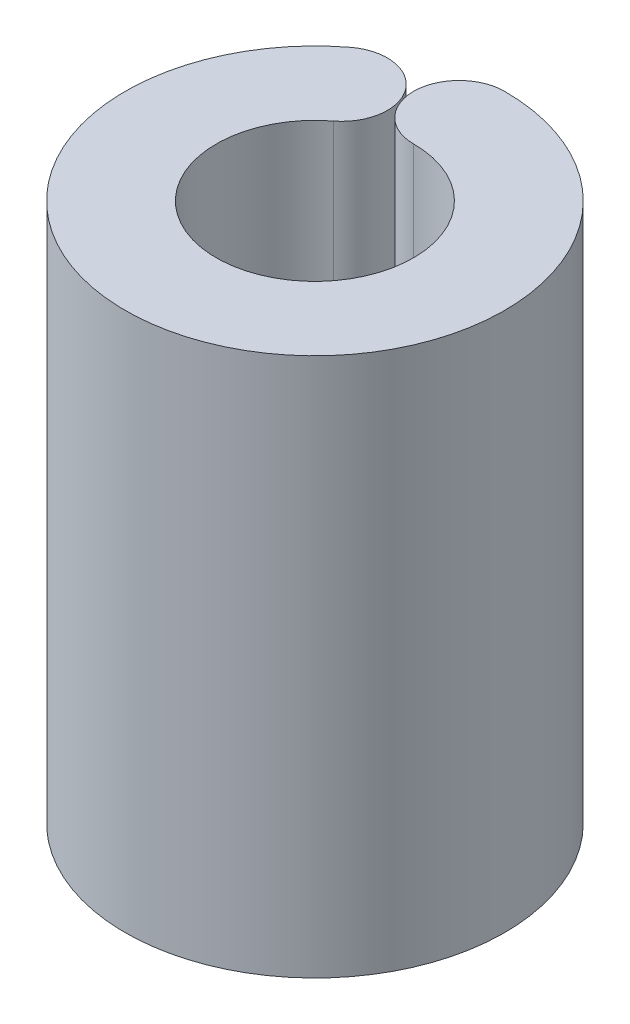
SolidWorks part; units mm, degrees
ref_plane "Front Plane" through (0, 0, 0) normal (0, 0, 1) x (1, 0, 0)
ref_plane "Top Plane" through (0, 0, 0) normal (0, 1, 0) x (1, 0, 0)
ref_plane "Right Plane" through (0, 0, 0) normal (1, 0, 0) x (0, 0, -1)
sketch "Sketch1" plane through (0, 0, 0) normal (0, 1, 0) x (1, 0, 0)
  arc A0 (0, 3.8) -> (-2.3089, 3.0181) centre (0, 0) cw
  arc A1 (0, 2.6) -> (-1.5798, 2.065) centre (0, 0) cw
  arc A2 (0, 5) -> (-3.038, 3.9712) centre (0, 0) cw
  arc A3 (0, 2.6) -> (0, 5) centre (0, 3.8) cw
  arc A4 (-1.5798, 2.065) -> (-3.038, 3.9712) centre (-2.3089, 3.0181) ccw
  dimension "D1" = 3.8
  dimension "D2" = 1.2
  dimension "D3" = 1.2
extrude "Boss-Extrude1" add sketch "Sketch1" along normal blind 14.2
